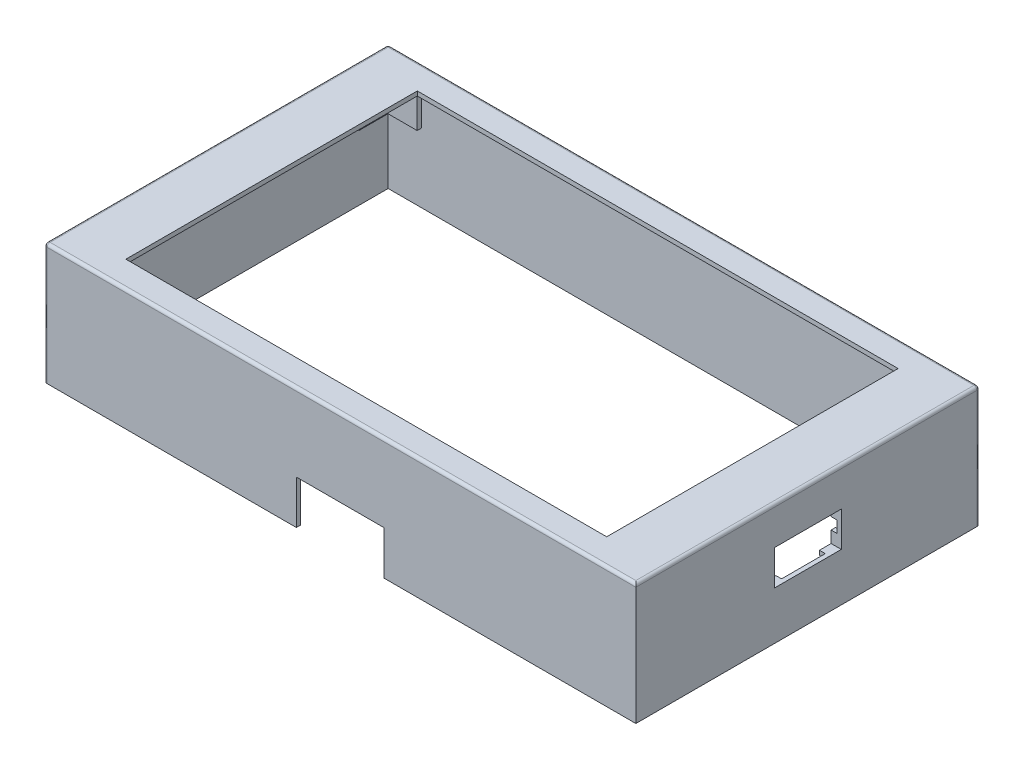
SolidWorks part; units mm, degrees
ref_plane "前视基准面" through (0, 0, 0) normal (0, 0, 1) x (1, 0, 0)
ref_plane "上视基准面" through (0, 0, 0) normal (0, 1, 0) x (1, 0, 0)
ref_plane "右视基准面" through (0, 0, 0) normal (1, 0, 0) x (0, 0, -1)
other "Configuration Table"
sketch "草图1" plane through (0, 0, 0) normal (0, 1, 0) x (1, 0, 0)
  line L1 (-82.5, 50) -> (82.5, 50) construction
  line L2 (-82.5, 50) -> (-82.5, -50) construction
  line L3 (-82.5, -50) -> (82.5, -50) construction
  line L4 (82.5, 50) -> (82.5, -50) construction
  line L5 (-82.5, 50) -> (82.5, -50) construction
  line L6 (-82.5, -50) -> (82.5, 50) construction
  line L7 (100, -57.5) -> (-100, -57.5)
  line L8 (100, -57.5) -> (100, 57.5)
  line L9 (100, 57.5) -> (-100, 57.5)
  line L10 (-100, -57.5) -> (-100, 57.5)
  line L11 (100, -57.5) -> (-100, 57.5) construction
  line L12 (100, 57.5) -> (-100, -57.5) construction
  point P0 (0, 0)
  point P6 (0, 0)
  dimension "D1" = 100
  dimension "D2" = 165
  dimension "D3" = 200
  dimension "D4" = 115
extrude "凸台-拉伸40mm" add sketch "草图1" along normal blind 40
ref_plane "基准面1" through (0, 40, 0) normal (0, 1, 0) x (1, 0, 0)
sketch "草图2" plane through (0, 40, 0) normal (0, 1, 0) x (1, 0, 0)
  line L0 (82.5, 50) -> (82.5, -50) construction
  line L1 (-82.5, -50) -> (82.5, -50) construction
  line L2 (-82.5, 50) -> (-82.5, -50) construction
  line L3 (-82.5, 50) -> (82.5, 50) construction
  line L4 (82.5, 50) -> (82.5, -50)
  line L5 (-82.5, -50) -> (82.5, -50)
  line L6 (-82.5, 50) -> (-82.5, -50)
  line L7 (-82.5, 50) -> (82.5, 50)
shell "抽壳3" thickness 1.5
extrude "切除-拉伸7" cut sketch "草图2" along normal blind 1.5
ref_plane "基准面2" through (-100, 0, 0) normal (1, 0, 0) x (0, 0, -1)
sketch "草图3" plane through (-100, 0, 0) normal (1, 0, 0) x (0, 0, -1)
  line L1 (50, 41.5) -> (-50, 41.5) construction
  line L2 (50, 41.5) -> (-50, 41.5) construction
  line L3 (37.9694, 32.5) -> (-16.0374, 32.5) construction
  line L4 (37.9694, 22.5) -> (-20.8388, 22.5) construction
  line L5 (50, 41.5) -> (50, 13.3792) construction
  line L6 (20, 5.8143) -> (20, 79.2673) construction
  line L7 (20, 22.5) -> (20, 32.5)
  line L8 (4, 32.5) -> (4, 22.5)
  line L9 (4, 22.5) -> (20, 22.5)
  line L10 (20, 32.5) -> (4, 32.5)
  dimension "D1" = 9
  dimension "D2" = 10
  dimension "D3" = 30
  dimension "D4" = 16
extrude "切除-拉伸8" cut sketch "草图3" against normal blind 1.5
ref_plane "基准面3" through (100, 0, 0) normal (-1, 0, 0) x (0, 0, 1)
sketch "草图4" plane through (100, 0, 0) normal (-1, 0, 0) x (0, 0, 1)
  line L0 (50, 41.5) -> (-50, 41.5) construction
  line L1 (50, 41.5) -> (-50, 41.5) construction
  line L2 (-59, 41.5) -> (-59, 0) construction
  line L3 (-59, 41.5) -> (-59, 0) construction
  line L4 (-59, 20.75) -> (56.2233, 20.75) construction
  line L5 (0, 41.5) -> (0, -21.6986) construction
  line L6 (-11.5, 16.5) -> (11.5, 28.5) construction
  line L7 (-11.5, 28.5) -> (11.5, 28.5)
  line L8 (-11.5, 28.5) -> (-11.5, 16.5)
  line L9 (-11.5, 16.5) -> (11.5, 16.5)
  line L10 (11.5, 28.5) -> (11.5, 16.5)
  line L11 (-11.5, 28.5) -> (11.5, 16.5) construction
  point P13 (0, 22.5)
  dimension "D1" = 63.1986
  dimension "D2" = 13
  dimension "D3" = 12
  dimension "D4" = 23
extrude "切除-拉伸9" cut sketch "草图4" against normal blind 1.5
ref_plane "基准面4" through (0, 40, 0) normal (0, -1, 0) x (-1, 0, 0)
sketch "草图6" plane through (0, 40, 0) normal (0, -1, 0) x (-1, 0, 0)
  line L0 (-44.1359, 0) -> (40.9262, 0) construction
  line L1 (-95.25, -52.7) -> (95.25, -52.7) construction
  line L2 (-95.25, -52.7) -> (-95.25, 52.7) construction
  line L3 (-95.25, 52.7) -> (95.25, 52.7) construction
  line L4 (95.25, -52.7) -> (95.25, 52.7) construction
  line L5 (-95.25, -52.7) -> (95.25, 52.7) construction
  line L6 (-95.25, 52.7) -> (95.25, -52.7) construction
  line L7 (0, 35.4902) -> (0, -35.4611) construction
  line L8 (-95.25, 52.7) -> (-85.25, 52.7)
  line L9 (-85.25, 52.7) -> (-85.25, 54.2)
  line L10 (-85.25, 54.2) -> (-96.75, 54.2)
  line L11 (-96.75, 54.2) -> (-96.75, 42.7)
  line L12 (-96.75, 42.7) -> (-95.25, 42.7)
  line L13 (-95.25, 42.7) -> (-95.25, 52.7)
  line L14 (-96.75, -42.7) -> (-95.25, -42.7)
  line L15 (-85.25, -52.7) -> (-85.25, -54.2)
  line L16 (-96.75, -54.2) -> (-96.75, -42.7)
  line L17 (-85.25, -54.2) -> (-96.75, -54.2)
  line L18 (-95.25, -52.7) -> (-85.25, -52.7)
  line L19 (-95.25, -42.7) -> (-95.25, -52.7)
  line L20 (85.25, -52.7) -> (85.25, -54.2)
  line L21 (85.25, -54.2) -> (96.75, -54.2)
  line L22 (95.25, -52.7) -> (85.25, -52.7)
  line L23 (95.25, -42.7) -> (95.25, -52.7)
  line L24 (96.75, -54.2) -> (96.75, -42.7)
  line L25 (96.75, -42.7) -> (95.25, -42.7)
  line L26 (85.25, 52.7) -> (85.25, 54.2)
  line L27 (96.75, 42.7) -> (95.25, 42.7)
  line L28 (95.25, 52.7) -> (85.25, 52.7)
  line L29 (95.25, 42.7) -> (95.25, 52.7)
  line L30 (96.75, 54.2) -> (96.75, 42.7)
  line L31 (85.25, 54.2) -> (96.75, 54.2)
  point P0 (0, 0)
  dimension "D1" = 190.5
  dimension "D2" = 105.4
  dimension "D3" = 1.5
  dimension "D4" = 1.5
  dimension "D5" = 10
  dimension "D6" = 10
extrude "凸台-拉伸1" add sketch "草图6" along normal blind 13
ref_plane "基准面5" through (100, 0, 0) normal (-1, 0, 0) x (0, 0, 1)
sketch "草图7" plane through (100, 0, 0) normal (-1, 0, 0) x (0, 0, 1)
  line L0 (57.5, 40) -> (-57.5, 40) construction
  line L1 (-11.5, 16.5) -> (11.5, 16.5) construction
  line L2 (11.5, 28.5) -> (11.5, 16.5) construction
  line L3 (-11.5, 28.5) -> (11.5, 28.5) construction
  line L4 (-11.5, 28.5) -> (-11.5, 16.5) construction
  line L5 (57.5, 40) -> (-57.5, 40) construction
  line L6 (-11.5, 16.5) -> (11.5, 16.5) construction
  line L7 (11.5, 28.5) -> (11.5, 16.5) construction
  line L8 (-11.5, 28.5) -> (11.5, 28.5) construction
  line L9 (-11.5, 28.5) -> (-11.5, 16.5) construction
  line L10 (50, 41.5) -> (-50, 41.5) construction
  line L11 (50, 41.5) -> (-50, 41.5) construction
  line L12 (13, 10.5) -> (11.5, 10.5) construction
  line L13 (-7.5, 28.5) -> (-7.5, 30)
  line L14 (-7.5, 30) -> (-13, 30)
  line L15 (-13, 30) -> (-13, 24.5)
  line L16 (-13, 24.5) -> (-11.5, 24.5)
  line L17 (-11.5, 24.5) -> (-11.5, 28.5)
  line L18 (-11.5, 28.5) -> (-7.5, 28.5)
  line L19 (0, 28.5) -> (0, 16.5) construction
  line L20 (-3.0917, 17.5) -> (3.5005, 17.5) construction
  line L21 (7.5, 28.5) -> (7.5, 30)
  line L22 (11.5, 28.5) -> (7.5, 28.5)
  line L23 (11.5, 24.5) -> (11.5, 28.5)
  line L24 (13, 24.5) -> (11.5, 24.5)
  line L25 (13, 30) -> (13, 24.5)
  line L26 (7.5, 30) -> (13, 30)
  line L27 (13, 5) -> (13, 10.5) construction
  line L28 (11.5, 10.5) -> (11.5, 6.5) construction
  line L29 (11.5, 6.5) -> (7.5, 6.5) construction
  line L30 (7.5, 6.5) -> (7.5, 5) construction
  line L31 (7.5, 5) -> (13, 5) construction
  line L32 (-7.5, 6.5) -> (-7.5, 5) construction
  line L33 (-11.5, 6.5) -> (-7.5, 6.5) construction
  line L34 (-11.5, 10.5) -> (-11.5, 6.5) construction
  line L35 (-13, 10.5) -> (-11.5, 10.5) construction
  line L36 (-13, 5) -> (-13, 10.5) construction
  line L37 (-7.5, 5) -> (-13, 5) construction
  line L38 (0, 22.5) -> (-3.575, 22.5) construction
  line L39 (-3.575, 22.5) -> (3.5005, 22.5) construction
  line L40 (7.5, 16.5) -> (7.5, 15)
  line L41 (-13, 20.5) -> (-11.5, 20.5)
  line L42 (-11.5, 20.5) -> (-11.5, 16.5)
  line L43 (-13, 15) -> (-13, 20.5)
  line L44 (-7.5, 16.5) -> (-7.5, 15)
  line L45 (-11.5, 16.5) -> (-7.5, 16.5)
  line L46 (-7.5, 15) -> (-13, 15)
  line L47 (13, 20.5) -> (11.5, 20.5)
  line L48 (11.5, 16.5) -> (7.5, 16.5)
  line L49 (11.5, 20.5) -> (11.5, 16.5)
  line L50 (13, 15) -> (13, 20.5)
  line L51 (7.5, 15) -> (13, 15)
  dimension "D1" = 1.5
  dimension "D2" = 1.5
  dimension "D3" = 4
  dimension "D4" = 4
extrude "凸台-拉伸2" add sketch "草图7" along normal blind 2
fillet "圆角2" radius 1 8 edges at (100, 20, 57.5) (0, 41.5, 59) (-101.5, 20.75, 59) (101.5, 41.5, 0) (101.5, 20.75, -59) (-101.5, 41.5, 0) (-101.5, 20.75, -59) (0, 41.5, -59)
ref_plane "基准面6" through (0, 0, 57.5) normal (0, 0, -1) x (-1, 0, 0)
sketch "草图9" plane through (0, 0, 57.5) normal (0, 0, -1) x (-1, 0, 0)
  line L1 (-15, -15) -> (15, -15)
  line L2 (-15, -15) -> (-15, 15)
  line L3 (-15, 15) -> (15, 15)
  line L4 (100, 40) -> (-99, 40)
  line L5 (-99, 40) -> (-99, 0)
  line L6 (-99, 0) -> (100, 0)
  line L7 (100, 0) -> (100, 40)
  line L8 (100, 40) -> (-99, 40) construction
  line L9 (-99, 40) -> (-99, 0) construction
  line L10 (-99, 0) -> (100, 0) construction
  line L11 (100, 0) -> (100, 40) construction
  line L12 (15, -15) -> (15, 15)
  line L13 (-15, -15) -> (15, 15) construction
  line L14 (-15, 15) -> (15, -15) construction
  point P2 (0, 0)
  dimension "D2" = 30
  dimension "D3" = 30
  dimension "D1" = 0
extrude "切除-拉伸10" cut sketch "草图9" against normal blind 10
